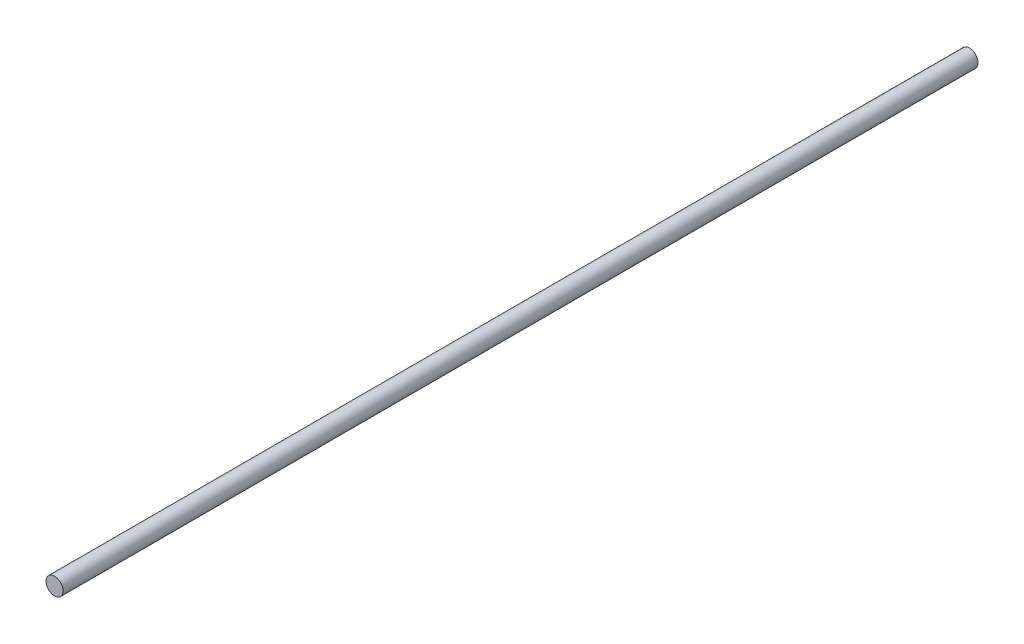
SolidWorks part; units mm, degrees
material "AISI Type A2 Tool Steel"
ref_plane "Front Plane" through (0, 0, 0) normal (0, 0, 1) x (1, 0, 0)
ref_plane "Top Plane" through (0, 0, 0) normal (0, 1, 0) x (1, 0, 0)
ref_plane "Right Plane" through (0, 0, 0) normal (1, 0, 0) x (0, 0, -1)
sketch "Sketch1" plane through (0, 0, 0) normal (0, 0, 1) x (1, 0, 0)
  circle A0 centre (0, 0) radius 3
  dimension "D1" = 6
extrude "Boss-Extrude1" add sketch "Sketch1" along normal blind 320
